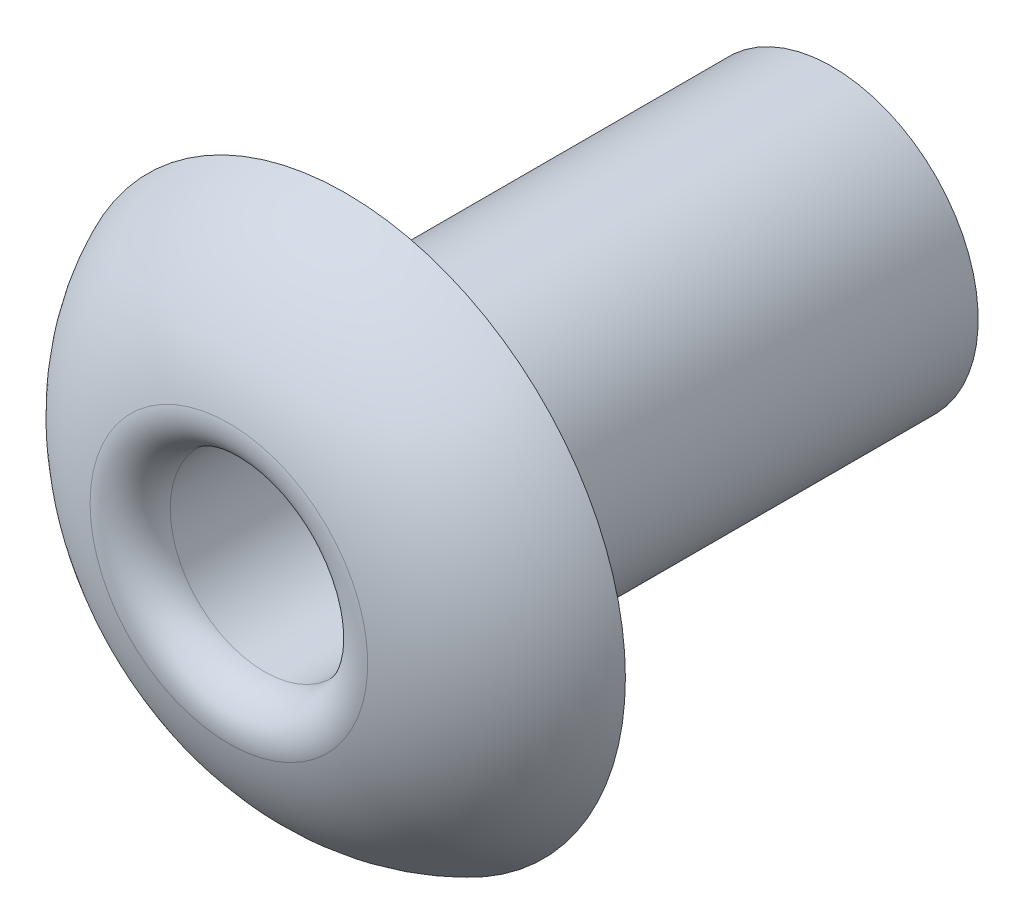
SolidWorks part; units mm, degrees
material "AISI 304"
ref_plane "前视基准面" through (0, 0, 0) normal (0, 0, 1) x (1, 0, 0)
ref_plane "上视基准面" through (0, 0, 0) normal (0, 1, 0) x (1, 0, 0)
ref_plane "右视基准面" through (0, 0, 0) normal (1, 0, 0) x (0, 0, -1)
sketch "草图1" plane through (0, 0, 0) normal (1, 0, 0) x (0, 0, -1)
  line L0 (0, 1.2) -> (0, 2.3)
  line L1 (0, 1.2) -> (4, 1.2)
  line L2 (4, 1.2) -> (4, 0.775)
  line L3 (4, 0) -> (0, 0) construction
  line L4 (-1, 0) -> (-1, -1.4133) construction
  line L5 (4, 0.775) -> (-1, 0.775)
  line L6 (-1, 0) -> (-1, 0.775) construction
  arc A0 (0, 2.3) -> (-1, 0.775) centre (0.6628, 0.775) ccw
  dimension "D1" = 4.6
  dimension "D2" = 1
  dimension "D3" = 4
  dimension "D4" = 1.55
  dimension "D5" = 2.4
revolve "旋转1" add sketch "草图1" angle 360 about L3
fillet "装饰圆角" radius 0.3 1 edges at (-0.775, 0, 1)
